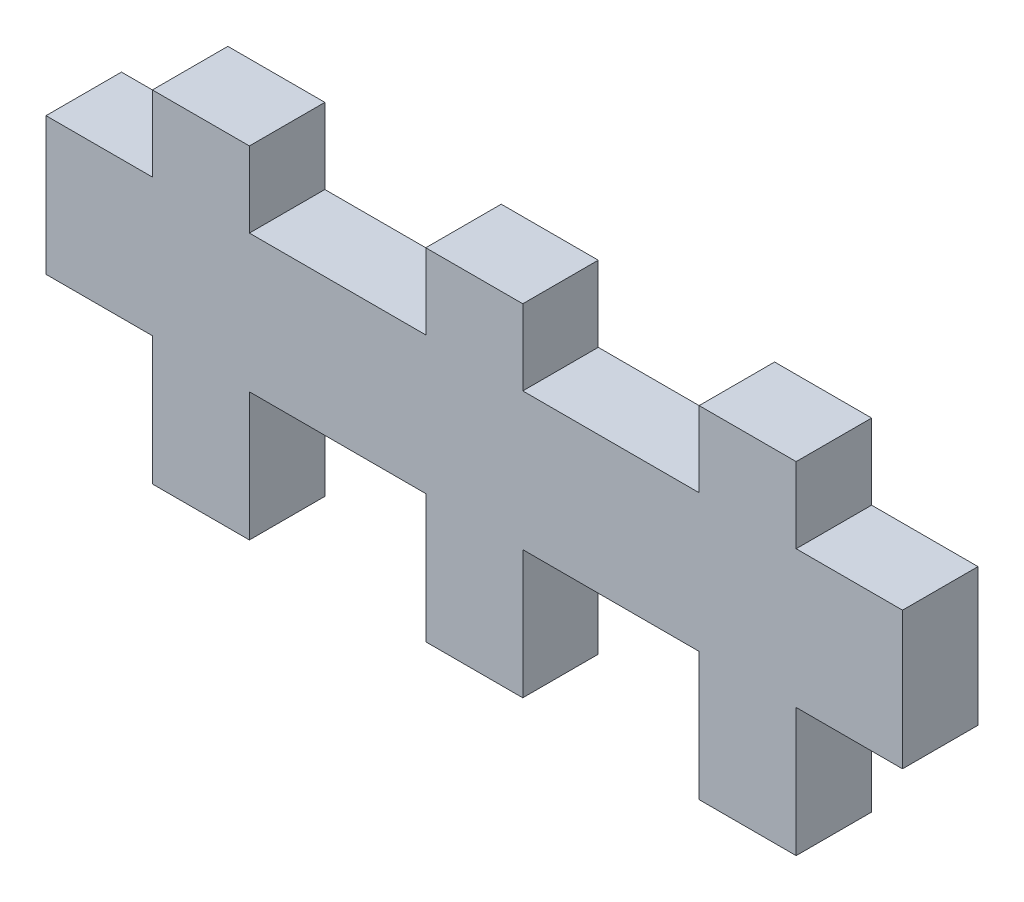
SolidWorks part; units mm, degrees
ref_plane "Front Plane" through (0, 0, 0) normal (0, 0, 1) x (1, 0, 0)
ref_plane "Top Plane" through (0, 0, 0) normal (0, 1, 0) x (1, 0, 0)
ref_plane "Right Plane" through (0, 0, 0) normal (1, 0, 0) x (0, 0, -1)
sketch "Sketch1" plane through (0, 0, 0) normal (0, 0, 1) x (1, 0, 0)
  line L2 (-21.15, 2.85) -> (21.15, 2.85) construction
  line L3 (-21.15, 0) -> (21.15, 0)
  line L4 (-21.15, 0) -> (-21.15, 5.7)
  line L5 (-21.15, 5.7) -> (21.15, 5.7)
  line L6 (21.15, 0) -> (21.15, 5.7)
  line L9 (-2, 8.875) -> (2, 5.7) construction
  line L16 (-2, 5.7) -> (2, 8.875) construction
  line L17 (2, 5.7) -> (2, 8.875)
  line L18 (-2, 0) -> (-2, -3.175)
  line L19 (-13.5, 0) -> (-13.5, -3.175)
  line L20 (-13.5, -3.175) -> (-9.5, -3.175)
  line L21 (-9.5, 0) -> (-9.5, -3.175)
  line L22 (13.5, 0) -> (13.5, -3.175)
  line L23 (13.5, -3.175) -> (9.5, -3.175)
  line L24 (9.5, 0) -> (9.5, -3.175)
  line L25 (-2, -3.175) -> (2, -3.175)
  line L26 (2, 0) -> (2, -3.175)
  line L27 (-2, 0) -> (2, -3.175) construction
  line L28 (-2, -3.175) -> (2, 0) construction
  line L29 (-2, 0) -> (2, 0)
  line L31 (-2, 8.875) -> (2, 8.875)
  line L32 (9.5, 5.7) -> (9.5, 8.875)
  line L43 (13.5, 8.875) -> (9.5, 8.875)
  line L44 (13.5, 5.7) -> (13.5, 8.875)
  line L48 (-9.5, 5.7) -> (-9.5, 8.875)
  line L49 (-13.5, 8.875) -> (-9.5, 8.875)
  line L50 (-13.5, 5.7) -> (-13.5, 8.875)
  line L51 (-2, 5.7) -> (-2, 8.875)
  line L52 (-2, -5.4) -> (2, -5.4)
  line L53 (-13.5, -3.175) -> (-9.5, -3.175)
  line L54 (-13.5, -3.175) -> (-13.5, -5.4)
  line L55 (-13.5, -5.4) -> (-9.5, -5.4)
  line L56 (-9.5, -3.175) -> (-9.5, -5.4)
  line L57 (2, -3.175) -> (2, -5.4)
  line L58 (-2, -3.175) -> (-2, -5.4)
  line L59 (9.5, -5.4) -> (13.5, -5.4)
  line L60 (13.5, -3.175) -> (13.5, -5.4)
  line L61 (9.5, -3.175) -> (9.5, -5.4)
  point P4 (0, 0)
  point P19 (0, 7.2875)
  point P28 (0, -1.5875)
  point P33 (0, 0)
  dimension "D7" = 4
  dimension "D8" = 3.175
  dimension "D9" = 7.5
  dimension "D10" = 7.5
  dimension "D2" = 42.3
  dimension "D3" = 5.7
  dimension "D4" = 5.4
  dimension "D6" = 7.5
  dimension "D5" = 3
extrude "Boss-Extrude1" add sketch "Sketch1" along normal blind 3.175 contours L21 L3 L19 L20 | L50 L5 L48 L49 | L51 L5 L17 L31 | L26 L3 L18 L25 | L5 L44 L43 L32 | L3 L24 L23 L22 | L3 L6 L5 L4 | L56 L20 L54 L55 | L25 L58 L52 L57 | L23 L61 L59 L60
sketch "Sketch2" plane through (0, 5.7, 0) normal (0, 1, 0) x (1, 0, 0)
  line L0 (-21.15, -3.175) -> (-13.5, -3.175) construction
  line L1 (-21.15, 0) -> (-17.975, 0)
  line L2 (-21.15, 0) -> (-21.15, -3.175)
  line L3 (-21.15, -3.175) -> (-17.975, -3.175)
  line L4 (-17.975, 0) -> (-17.975, -3.175)
  line L5 (13.5, -3.175) -> (21.15, -3.175) construction
  line L6 (21.15, 0) -> (17.975, 0)
  line L7 (21.15, 0) -> (21.15, -3.175)
  line L8 (21.15, -3.175) -> (17.975, -3.175)
  line L9 (17.975, 0) -> (17.975, -3.175)
  line L10 (-21.15, -3.175) -> (-17.975, 0)
  line L11 (21.15, -3.175) -> (17.975, 0)
  line M4 (-13.5, 0) -> (-21.15, 0)
  line M5 (-21.15, 0) -> (-21.15, -3.175)
  line M6 (-21.15, -3.175) -> (-13.5, -3.175)
  dimension "D1" = 3.175
  dimension "D2" = 3.175
extrude "Cut-Extrude2" cut sketch "Sketch2" against normal blind 23.175 contours L10 M5 M4 | L10 L4 M6 | L8 L11 L9 | L11 L7 L6
sketch "Sketch3" plane through (0, 0, 3.175) normal (0, 0, 1) x (1, 0, 0)
  line L28 (-13.5406, -5.4406) -> (-9.4594, -5.4406)
  line L29 (-13.5406, -5.4406) -> (-9.4594, -5.4406)
  line L30 (-2.0406, -5.4406) -> (2.0406, -5.4406)
  line L31 (-2.0406, -5.4406) -> (2.0406, -5.4406)
  line L32 (9.4594, -5.4406) -> (13.5406, -5.4406)
  line L33 (9.4594, -5.4406) -> (13.5406, -5.4406)
  line L56 (-13.5406, 5.7406) -> (-18.0156, 5.7406)
  line L57 (-18.0156, 5.7406) -> (-18.0156, -0.0406)
  line L58 (-18.0156, -0.0406) -> (-13.5406, -0.0406)
  line L59 (-13.5406, -0.0406) -> (-13.5406, -5.4406)
  line L61 (-9.4594, -5.4406) -> (-9.4594, -0.0406)
  line L62 (-9.4594, -0.0406) -> (-2.0406, -0.0406)
  line L63 (-2.0406, -0.0406) -> (-2.0406, -5.4406)
  line L65 (2.0406, -5.4406) -> (2.0406, -0.0406)
  line L66 (2.0406, -0.0406) -> (9.4594, -0.0406)
  line L67 (9.4594, -0.0406) -> (9.4594, -5.4406)
  line L69 (13.5406, -5.4406) -> (13.5406, -0.0406)
  line L70 (13.5406, -0.0406) -> (18.0156, -0.0406)
  line L71 (18.0156, -0.0406) -> (18.0156, 5.7406)
  line L72 (18.0156, 5.7406) -> (13.5406, 5.7406)
  line L73 (13.5406, 5.7406) -> (13.5406, 8.9156)
  line L74 (13.5406, 8.9156) -> (9.4594, 8.9156)
  line L75 (9.4594, 8.9156) -> (9.4594, 5.7406)
  line L76 (9.4594, 5.7406) -> (2.0406, 5.7406)
  line L77 (2.0406, 5.7406) -> (2.0406, 8.9156)
  line L78 (2.0406, 8.9156) -> (-2.0406, 8.9156)
  line L79 (-2.0406, 8.9156) -> (-2.0406, 5.7406)
  line L80 (-2.0406, 5.7406) -> (-9.4594, 5.7406)
  line L81 (-9.4594, 5.7406) -> (-9.4594, 8.9156)
  line L82 (-9.4594, 8.9156) -> (-13.5406, 8.9156)
  line L83 (-13.5406, 8.9156) -> (-13.5406, 5.7406)
  line L84 (-13.5406, 5.7406) -> (-18.0156, 5.7406)
  line L85 (-18.0156, 5.7406) -> (-18.0156, -0.0406)
  line L86 (-18.0156, -0.0406) -> (-13.5406, -0.0406)
  line L87 (-13.5406, -0.0406) -> (-13.5406, -5.4406)
  line L89 (-9.4594, -5.4406) -> (-9.4594, -0.0406)
  line L90 (-9.4594, -0.0406) -> (-2.0406, -0.0406)
  line L91 (-2.0406, -0.0406) -> (-2.0406, -5.4406)
  line L93 (2.0406, -5.4406) -> (2.0406, -0.0406)
  line L94 (2.0406, -0.0406) -> (9.4594, -0.0406)
  line L95 (9.4594, -0.0406) -> (9.4594, -5.4406)
  line L97 (13.5406, -5.4406) -> (13.5406, -0.0406)
  line L98 (13.5406, -0.0406) -> (18.0156, -0.0406)
  line L99 (18.0156, -0.0406) -> (18.0156, 5.7406)
  line L100 (18.0156, 5.7406) -> (13.5406, 5.7406)
  line L101 (13.5406, 5.7406) -> (13.5406, 8.9156)
  line L102 (13.5406, 8.9156) -> (9.4594, 8.9156)
  line L103 (9.4594, 8.9156) -> (9.4594, 5.7406)
  line L104 (9.4594, 5.7406) -> (2.0406, 5.7406)
  line L105 (2.0406, 5.7406) -> (2.0406, 8.9156)
  line L106 (2.0406, 8.9156) -> (-2.0406, 8.9156)
  line L107 (-2.0406, 8.9156) -> (-2.0406, 5.7406)
  line L108 (-2.0406, 5.7406) -> (-9.4594, 5.7406)
  line L109 (-9.4594, 5.7406) -> (-9.4594, 8.9156)
  line L110 (-9.4594, 8.9156) -> (-13.5406, 8.9156)
  line L111 (-13.5406, 8.9156) -> (-13.5406, 5.7406)
  dimension "D1" = 0.0406
extrude "Boss-Extrude2" add sketch "Sketch3" against normal blind 3.175
equation "\"stepper width\"=4.23"
equation "\"stepper hole disctance\"= 3.1"
equation "\"stepper hole diameter\"=0.34"
equation "\"stepper shaft hole\"=2.4"
equation "\"tooth width\"=0.4"
equation "\"tooth thickness\"=0.3175"
equation "\"tooth to side\"=0.75"
equation "\"motor chamber height\"= 6"
equation "\"D2@Sketch1\"=\"stepper width\""
equation "\"D1@Sketch2\"=\"tooth thickness\""
equation "\"D2@Sketch2\"=\"tooth thickness\""
